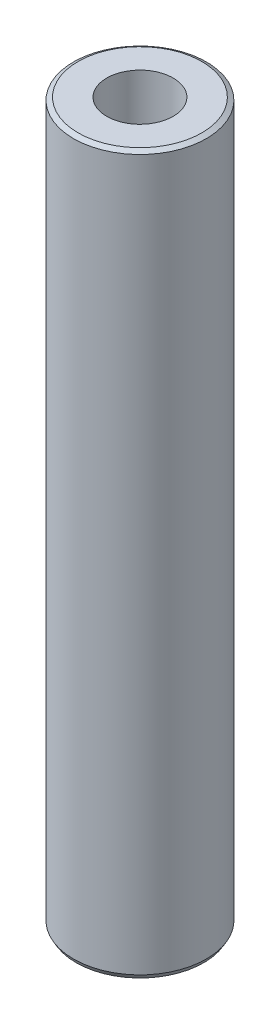
SolidWorks part; units mm, degrees
ref_plane "Front Plane" through (0, 0, 0) normal (0, 0, 1) x (1, 0, 0)
ref_plane "Top Plane" through (0, 0, 0) normal (0, 1, 0) x (1, 0, 0)
ref_plane "Right Plane" through (0, 0, 0) normal (1, 0, 0) x (0, 0, -1)
sketch "Sketch2" plane through (0, 0, 0) normal (0, 1, 0) x (1, 0, 0)
  circle A0 centre (0, 0) radius 2.5
  dimension "D1" = 5
extrude "Boss-Extrude1" add sketch "Sketch2" along normal blind 27
chamfer "Chamfer1" distance 0.1 angle 60 2 edges at (0, 0, 2.5) (0, 27, 2.5)
hole_wizard "M3x0.5 Tapped Hole1" positions "Sketch3" profile "Sketch4" tap size "M3x0.5" standard "ANSI Metric" end condition through all
sketch "Sketch3" plane through (0, 27, 0) normal (0, 1, 0) x (1, 0, 0)
  point P0 (0, 0)
sketch "Sketch4" plane through (0, 27, 0) normal (1, 0, 0) x (0, 0, 1)
  line L0 (0, 0) -> (0, 27)
  line L1 (0, 27) -> (1.25, 27)
  line L2 (1.25, 27) -> (1.25, 0)
  line L5 (1.25, 0) -> (0, 0)
  line L11 (0, -6.35) -> (0, 107.95) construction
  dimension "Thru Tap Drill Dia." = 2.5
  dimension "Thru Tap Drill Depth" = 27
cosmetic thread "Hole Thread1"
